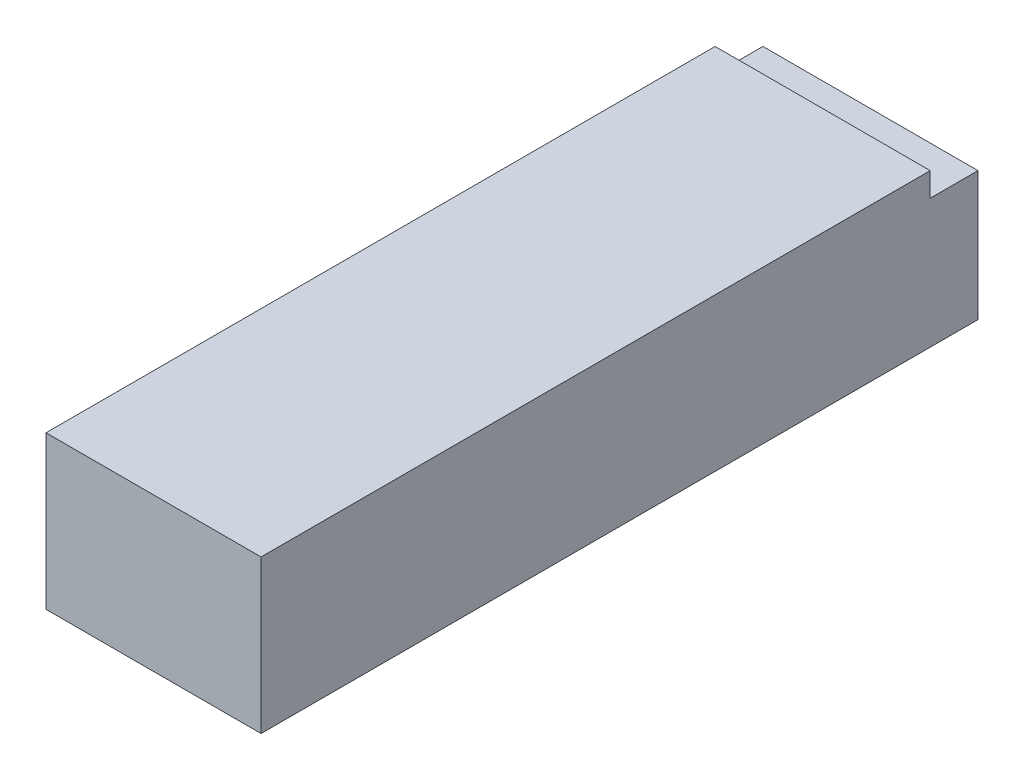
SolidWorks part; units mm, degrees
ref_plane "Front Plane" through (0, 0, 0) normal (0, 0, 1) x (1, 0, 0)
ref_plane "Top Plane" through (0, 0, 0) normal (0, 1, 0) x (1, 0, 0)
ref_plane "Right Plane" through (0, 0, 0) normal (1, 0, 0) x (0, 0, -1)
sketch "Sketch1" plane through (0, 0, 0) normal (0, 0, 1) x (1, 0, 0)
  line L1 (-22.5, 16) -> (22.5, 16)
  line L2 (-22.5, 16) -> (-22.5, -16)
  line L3 (-22.5, -16) -> (22.5, -16)
  line L4 (22.5, 16) -> (22.5, -16)
  line L5 (-22.5, 16) -> (22.5, -16) construction
  line L6 (-22.5, -16) -> (22.5, 16) construction
  point P0 (0, 0)
  dimension "D1" = 45
  dimension "D2" = 32
extrude "Boss-Extrude1" add sketch "Sketch1" along normal blind 150
sketch "Sketch2" plane through (0, 16, 0) normal (0, 1, 0) x (1, 0, 0)
  line L1 (-22.5, -10) -> (22.5, -10)
  line L2 (-22.5, -10) -> (-22.5, 0)
  line L3 (-22.5, 0) -> (22.5, 0)
  line L4 (22.5, -10) -> (22.5, 0)
  line L5 (-22.5, -10) -> (22.5, 0) construction
  line L6 (-22.5, 0) -> (22.5, -10) construction
  point P0 (0, -5)
  dimension "D1" = 10
extrude "Cut-Extrude1" cut sketch "Sketch2" against normal blind 5
